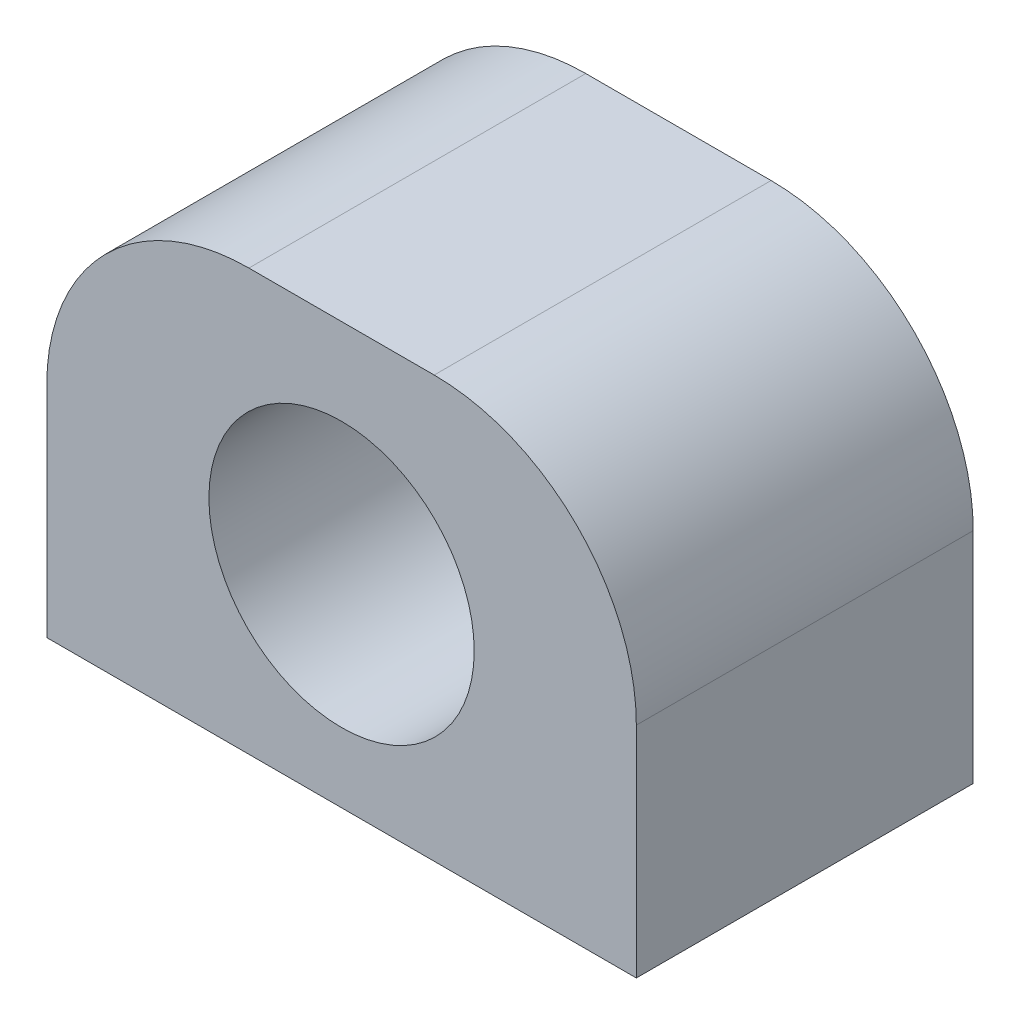
SolidWorks part; units mm, degrees
ref_plane "Front Plane" through (0, 0, 0) normal (0, 0, 1) x (1, 0, 0)
ref_plane "Top Plane" through (0, 0, 0) normal (0, 1, 0) x (1, 0, 0)
ref_plane "Right Plane" through (0, 0, 0) normal (1, 0, 0) x (0, 0, -1)
sketch "Sketch1" plane through (0, 0, 0) normal (0, 1, 0) x (1, 0, 0)
  line L1 (-16.3353, 9.1448) -> (18.6647, 9.1448)
  line L2 (-16.3353, 9.1448) -> (-16.3353, -10.8552)
  line L3 (-16.3353, -10.8552) -> (18.6647, -10.8552)
  line L4 (18.6647, 9.1448) -> (18.6647, -10.8552)
  dimension "D1" = 35
  dimension "D2" = 20
extrude "Boss-Extrude1" add sketch "Sketch1" along normal blind 25
sketch "Sketch2" plane through (0, 0, 10.8552) normal (0, 0, 1) x (1, 0, 0)
  line L0 (18.6647, 25) -> (18.6647, 0) construction
  line L1 (-16.3353, 0) -> (18.6647, 0) construction
  circle A0 centre (1.1647, 12) radius 7.875
  dimension "D1" = 17.5
  dimension "D2" = 12
extrude "Cut-Extrude1" cut sketch "Sketch2" against normal through all
sketch "Sketch3" plane through (0, 0, 0) normal (0, -1, 0) x (1, 0, 0)
  line L0 (18.6647, -9.1448) -> (-16.3353, -9.1448) construction
  line L1 (-16.3353, -9.1448) -> (-16.3353, 10.8552) construction
  line L2 (18.6647, 10.8552) -> (18.6647, -9.1448) construction
  circle A0 centre (-8.3353, 0.8552) radius 1.75
  circle A1 centre (10.6647, 0.8552) radius 1.75
  point P4 (-16.3353, 0.8552)
  dimension "D1" = 10
  dimension "D3" = 10
  dimension "D2" = 8
  dimension "D4" = 8
extrude "Cut-Extrude2" cut sketch "Sketch3" against normal blind 10
fillet "Fillet1" radius 12 2 edges at (18.6647, 25, 0.8552) (-16.3353, 25, 0.8552)
